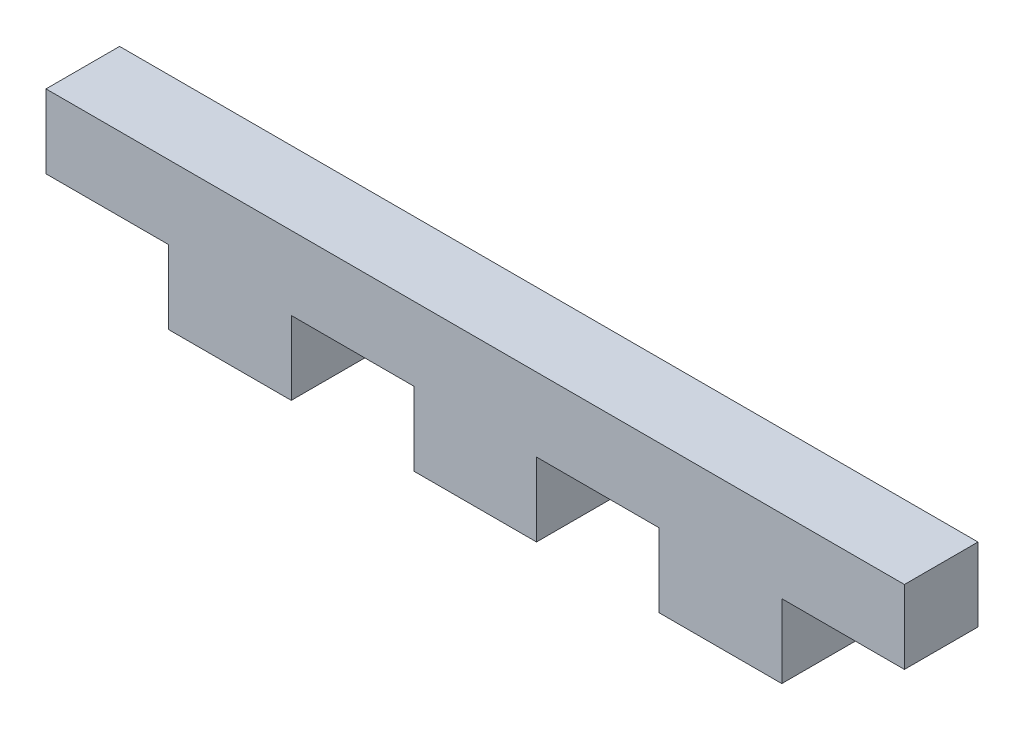
SolidWorks part; units mm, degrees
ref_plane "Plan de face" through (0, 0, 0) normal (0, 0, 1) x (1, 0, 0)
ref_plane "Plan de dessus" through (0, 0, 0) normal (0, 1, 0) x (1, 0, 0)
ref_plane "Plan de droite" through (0, 0, 0) normal (1, 0, 0) x (0, 0, -1)
sketch "Esquisse1" plane through (0, 0, 0) normal (0, 0, 1) x (1, 0, 0)
  line L0 (13.9901, 0.1004) -> (13.9901, -2.8996)
  line L1 (3.9901, 0.1004) -> (8.9901, 0.1004)
  line L2 (3.9901, 0.1004) -> (3.9901, -2.8996)
  line L3 (3.9901, -2.8996) -> (8.9901, -2.8996)
  line L4 (8.9901, 0.1004) -> (8.9901, -2.8996)
  line L5 (33.9901, 3.1004) -> (-1.0099, 3.1004)
  line L6 (33.9901, 3.1004) -> (33.9901, 0.1004)
  line L7 (33.9901, 0.1004) -> (-1.0099, 0.1004)
  line L8 (-1.0099, 3.1004) -> (-1.0099, 0.1004)
  line L9 (13.9901, -2.8996) -> (18.9901, -2.8996)
  line L10 (18.9901, 0.1004) -> (18.9901, -2.8996)
  line L11 (23.9901, 0.1004) -> (23.9901, -2.8996)
  line L12 (23.9901, -2.8996) -> (28.9901, -2.8996)
  line L13 (28.9901, 0.1004) -> (28.9901, -2.8996)
  dimension "D1" = 3
  dimension "D2" = 35
  dimension "D3" = 5
  dimension "D6" = 3
  dimension "D7" = 5
extrude "Boss.-Extru.1" add sketch "Esquisse1" along normal blind 3
